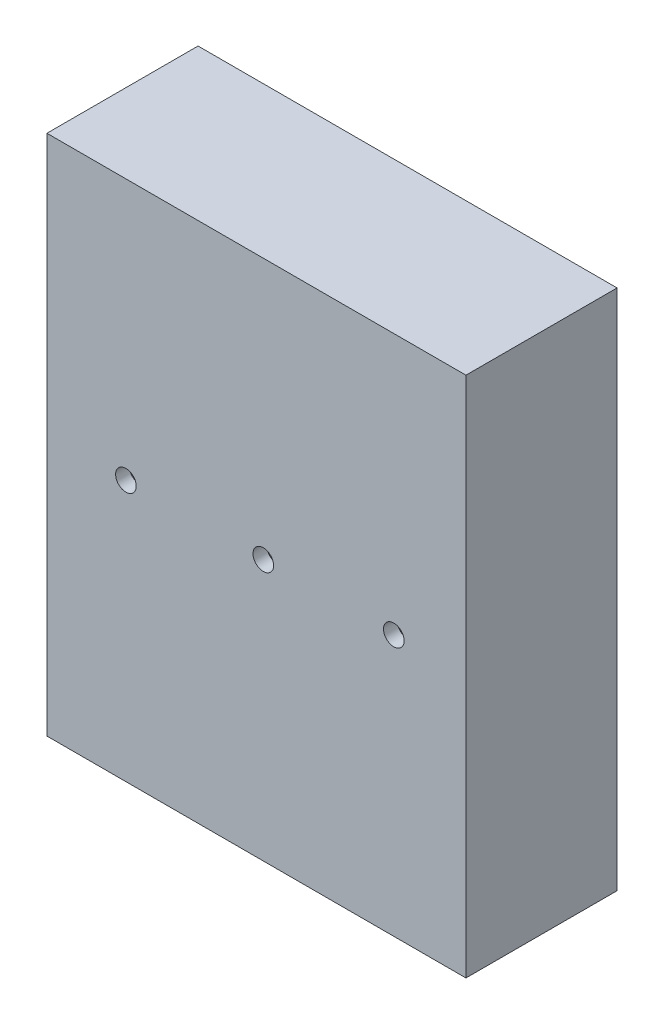
SolidWorks part; units mm, degrees
ref_plane "Front Plane" through (0, 0, 0) normal (0, 0, 1) x (1, 0, 0)
ref_plane "Top Plane" through (0, 0, 0) normal (0, 1, 0) x (1, 0, 0)
ref_plane "Right Plane" through (0, 0, 0) normal (1, 0, 0) x (0, 0, -1)
sketch "Sketch1" plane through (0, 0, 0) normal (0, 0, 1) x (1, 0, 0)
  line L0 (3, -3) -> (78, -3)
  line L1 (0, 0) -> (81, 0)
  line L2 (0, 0) -> (0, -76)
  line L3 (0, -76) -> (81, -76)
  line L4 (81, 0) -> (81, -76)
  line L5 (78, -3) -> (78, -73)
  line L6 (3, -73) -> (78, -73)
  line L7 (3, -3) -> (3, -73)
  line L9 (20, -3) -> (23, -3)
  line L10 (20, -3) -> (20, -73)
  line L11 (20, -73) -> (23, -73)
  line L12 (23, -3) -> (23, -73)
  line L13 (40, -3) -> (43, -3)
  line L14 (40, -3) -> (40, -73)
  line L15 (40, -73) -> (43, -73)
  line L16 (43, -3) -> (43, -73)
  line L17 (61, -3) -> (58, -3)
  line L18 (61, -3) -> (61, -73)
  line L19 (61, -73) -> (58, -73)
  line L20 (58, -3) -> (58, -73)
  line L21 (78, -73) -> (3, -73)
  line L22 (78, -73) -> (78, -3)
  line L23 (78, -3) -> (3, -3)
  line L24 (3, -73) -> (3, -3)
  point P9 (20, -3)
  point P10 (61, -3)
  point P15 (40, -3)
  dimension "D1" = 81
  dimension "D2" = 76
  dimension "D4" = 17
  dimension "D5" = 17
  dimension "D6" = 3
  dimension "D7" = 17
  dimension "D8" = 3
  dimension "D9" = 3
  dimension "D3" = 3
extrude "Boss-Extrude2" add sketch "Sketch1" along normal blind 20 contours L12 L0 L10 L6 | L16 L0 L14 L6 | L0 L20 L6 L18 | L4 L1 L2 L3 L7 L0 L5 L6
sketch "Sketch3" plane through (0, 0, 20) normal (0, 0, 1) x (1, 0, 0)
  line L1 (0, 0) -> (81, 0)
  line L2 (0, 0) -> (0, -76)
  line L3 (0, -76) -> (81, -76)
  line L4 (81, 0) -> (81, -76)
extrude "Boss-Extrude3" add sketch "Sketch3" along normal blind 2
sketch "Sketch4" plane through (0, 0, 20) normal (0, 0, -1) x (-1, 0, 0)
  line L0 (-20, -38) -> (-3, -38)
  line L1 (-3, -73) -> (-78, -73)
  line L2 (-3, -73) -> (-3, -3)
  line L3 (-3, -3) -> (-78, -3)
  line L4 (-78, -73) -> (-78, -3)
  line L5 (-20, -73) -> (-20, -3)
  line L6 (-61, -73) -> (-61, -3)
  line L7 (-61, -38) -> (-78, -38)
  line L8 (-23, -38) -> (-40, -38)
  line L9 (-23, -73) -> (-40, -73)
  line L10 (-23, -73) -> (-23, -3)
  line L11 (-23, -3) -> (-40, -3)
  line L12 (-40, -73) -> (-40, -3)
  line L13 (-43, -73) -> (-58, -73)
  line L14 (-43, -73) -> (-43, -3)
  line L15 (-43, -3) -> (-58, -3)
  line L16 (-58, -73) -> (-58, -3)
  line L17 (-43, -38) -> (-58, -38)
  circle A0 centre (-11.5, -38) radius 1.5
  circle A1 centre (-69.5, -38) radius 1.5
  circle A2 centre (-31.5, -38) radius 1.5
  circle A3 centre (-50.5, -38) radius 1.5
  dimension "D1" = 3
  dimension "D2" = 3
extrude "Cut-Extrude2" cut sketch "Sketch4" against normal blind 2 contours L0 A0 | L8 A2 | L8 A2 | L17 A3 | L17 A3 | L7 A1 | L7 A1
sketch "Sketch5" plane through (0, 0, 20) normal (0, 0, -1) x (-1, 0, 0)
  line L0 (-78, -3) -> (-78, -73) construction
  line L1 (-61, -73) -> (-78, -73)
  line L2 (-61, -73) -> (-61, -3)
  line L3 (-61, -3) -> (-78, -3)
  line L4 (-78, -73) -> (-78, -3)
  line L5 (-61, -73) -> (-61, -79.1253)
  line L6 (-61, -79.1253) -> (-89.8013, -78.4283)
  line L7 (-89.8013, -78.4283) -> (-91.2985, 3.586)
  line L8 (-91.2985, 3.586) -> (-61, 3.586)
  line L9 (-61, 3.586) -> (-61, -3)
  circle M4 centre (-69.5, -38) radius 1.5
  line M5 (-61, -73) -> (-61, -3)
  line M6 (-61, -3) -> (-78, -3)
  line M7 (-78, -3) -> (-78, -73)
  line M8 (-78, -73) -> (-61, -73)
extrude "Cut-Extrude3" cut sketch "Sketch5" against normal through all and the other way through all contours L9 L8 L7 L6 L5 M8 M7 M6 | M8 M5 M6 M7 M4
